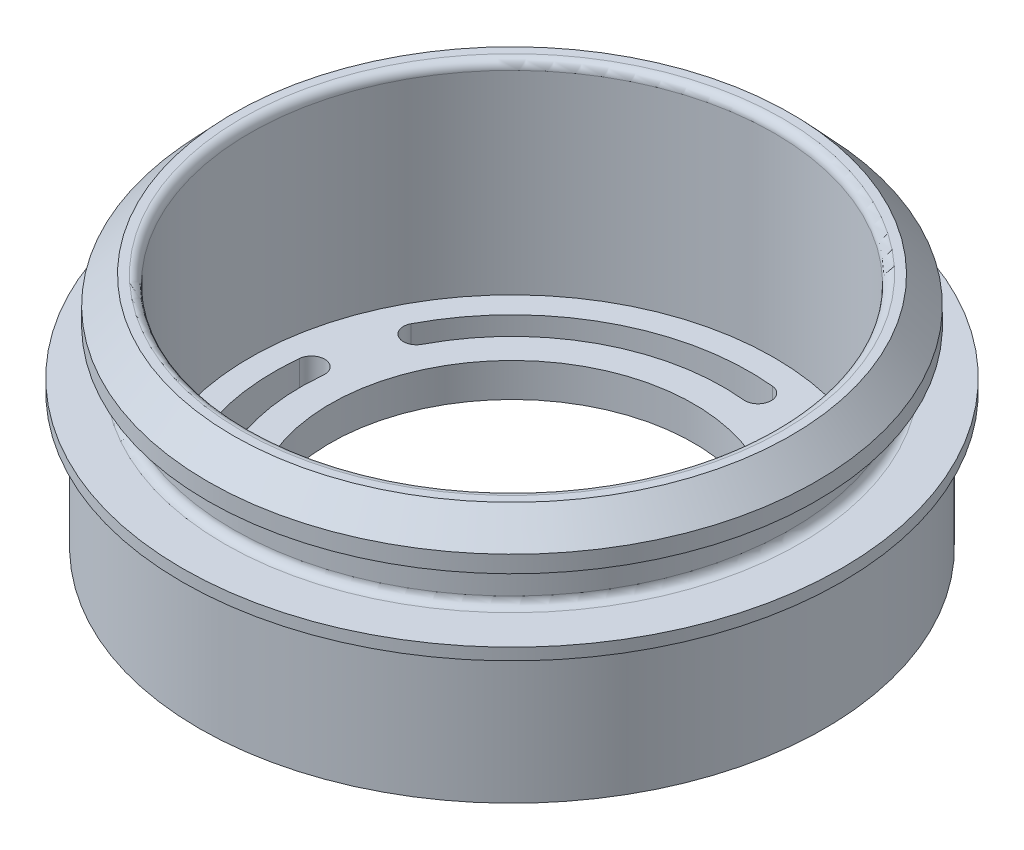
SolidWorks part; units mm, degrees
ref_plane "Front Plane" through (0, 0, 0) normal (0, 0, 1) x (1, 0, 0)
ref_plane "Top Plane" through (0, 0, 0) normal (0, 1, 0) x (1, 0, 0)
ref_plane "Right Plane" through (0, 0, 0) normal (1, 0, 0) x (0, 0, -1)
sketch "Sketch1" plane through (0, 0, 0) normal (0, 0, 1) x (1, 0, 0)
  line L0 (-16.5, 9.4) -> (-18, 9.4)
  line L1 (-16.5, 9.4) -> (-16.5, 7.2)
  line L2 (-17, 6.7) -> (-19.5, 6.7)
  line L3 (-19.5, 6.7) -> (-19.5, 6)
  line L4 (-19.5, 6) -> (-18.5, 6)
  line L5 (-18.5, 6) -> (-18.5, 0)
  line L7 (-15.5, 0) -> (-15.5, 11.5)
  line L8 (-16, 12) -> (-16.5, 12)
  line L9 (-16.5, 12) -> (-18, 10.4)
  line L10 (-18, 10.4) -> (-18, 9.4)
  line L11 (-15.5, 0) -> (-10.75, 0)
  line L12 (-10.75, 0) -> (-10.75, -2)
  line L13 (-10.75, -2) -> (-18.5, -2)
  line L14 (-18.5, -2) -> (-18.5, 0)
  arc A0 (-15.5, 11.5) -> (-16, 12) centre (-16, 11.5) ccw
  arc A1 (-16.5, 7.2) -> (-17, 6.7) centre (-17, 7.2) cw
  point P14 (-15.5, 12)
  dimension "D12" = 0.5
  dimension "D1" = 1
  dimension "D2" = 2.5
  dimension "D3" = 15.5
  dimension "D4" = 16.5
  dimension "D5" = 10.75
  dimension "D6" = 3
  dimension "D7" = 2.6
  dimension "D8" = 1
  dimension "D9" = 2.7
  dimension "D10" = 3
  dimension "D11" = 2
  dimension "D13" = 0
  dimension "D14" = 6
  dimension "D15" = 6.7
ref_axis "Axis1" through (0, 12.7, 0) along (0, -1, 0)
revolve "Revolve1" add sketch "Sketch1" angle 360 about axis through (0, 12.7, 0) along (0, -1, 0)
sketch "Sketch2" plane through (0, 0, 0) normal (0, 1, 0) x (1, 0, 0)
  arc A0 (-6.1316, -11.7741) -> (-13.2067, 1.3447) centre (0, 0) cw construction
  arc A1 (-13.9846, 1.4239) -> (-6.4927, -12.4676) centre (0, 0) ccw
  arc A2 (-12.4288, 1.2655) -> (-5.7704, -11.0806) centre (0, 0) ccw
  arc A3 (-12.4288, 1.2655) -> (-13.9846, 1.4239) centre (-13.2067, 1.3447) ccw
  arc A4 (-6.4927, -12.4676) -> (-5.7704, -11.0806) centre (-6.1316, -11.7741) ccw
  arc A5 (-11.7741, 6.1316) -> (1.3447, 13.2067) centre (0, 0) cw construction
  arc A6 (1.4239, 13.9846) -> (-12.4676, 6.4927) centre (0, 0) ccw
  arc A7 (1.2655, 12.4288) -> (-11.0806, 5.7704) centre (0, 0) ccw
  arc A8 (1.2655, 12.4288) -> (1.4239, 13.9846) centre (1.3447, 13.2067) ccw
  arc A9 (-12.4676, 6.4927) -> (-11.0806, 5.7704) centre (-11.7741, 6.1316) ccw
  arc A10 (6.1316, 11.7741) -> (13.2067, -1.3447) centre (0, 0) cw construction
  arc A11 (13.9846, -1.4239) -> (6.4927, 12.4676) centre (0, 0) ccw
  arc A12 (12.4288, -1.2655) -> (5.7704, 11.0806) centre (0, 0) ccw
  arc A13 (12.4288, -1.2655) -> (13.9846, -1.4239) centre (13.2067, -1.3447) ccw
  arc A14 (6.4927, 12.4676) -> (5.7704, 11.0806) centre (6.1316, 11.7741) ccw
  arc A15 (11.7741, -6.1316) -> (-1.3447, -13.2067) centre (0, 0) cw construction
  arc A16 (-1.4239, -13.9846) -> (12.4676, -6.4927) centre (0, 0) ccw
  arc A17 (-1.2655, -12.4288) -> (11.0806, -5.7704) centre (0, 0) ccw
  arc A18 (-1.2655, -12.4288) -> (-1.4239, -13.9846) centre (-1.3447, -13.2067) ccw
  arc A19 (12.4676, -6.4927) -> (11.0806, -5.7704) centre (11.7741, -6.1316) ccw
  point P4 (-11.6841, -6.3014)
  point P14 (-6.3014, 11.6841)
  point P21 (11.6841, 6.3014)
  point P28 (6.3014, -11.6841)
  point P33 (0, 0)
  dimension "D1" = 4
extrude "Cut-Extrude1" cut sketch "Sketch2" against normal up to next
